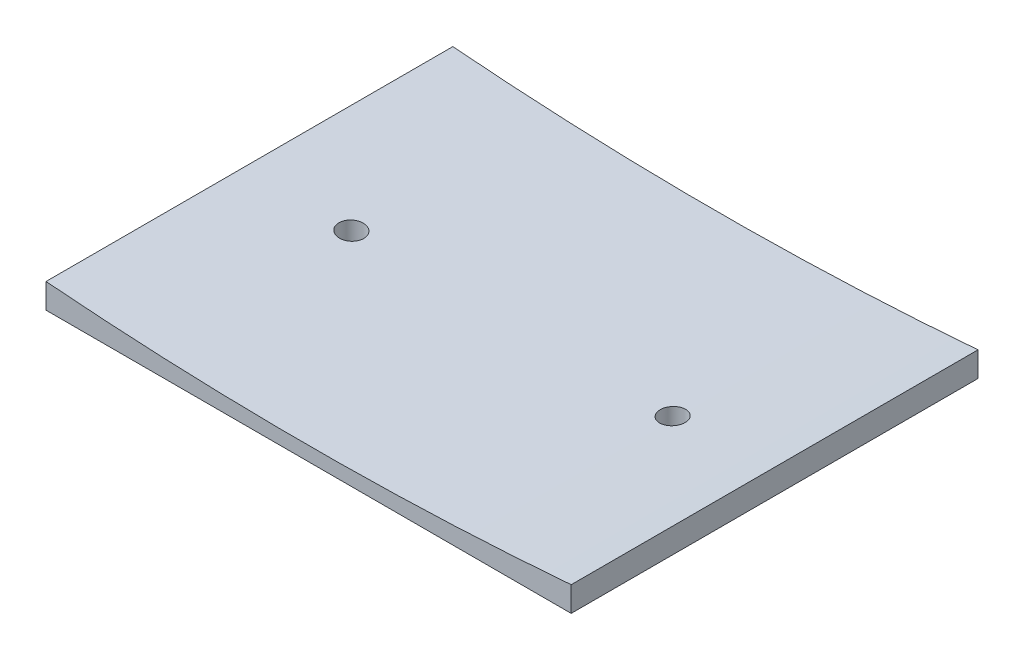
SolidWorks part; units mm, degrees
ref_plane "Alzado" through (0, 0, 0) normal (0, 0, 1) x (1, 0, 0)
ref_plane "Planta" through (0, 0, 0) normal (0, 1, 0) x (1, 0, 0)
ref_plane "Vista lateral" through (0, 0, 0) normal (1, 0, 0) x (0, 0, -1)
sketch "Croquis1" plane through (0, 0, 0) normal (0, 1, 0) x (1, 0, 0)
  line L1 (-18.6005, 9.0703) -> (34.1995, 9.0703)
  line L2 (-18.6005, 9.0703) -> (-18.6005, -31.8297)
  line L3 (-18.6005, -31.8297) -> (34.1995, -31.8297)
  line L4 (34.1995, 9.0703) -> (34.1995, -31.8297)
  dimension "D1" = 52.8
  dimension "D2" = 40.9
extrude "Saliente-Extruir1" add sketch "Croquis1" along normal blind 2.5
sketch "Croquis2" plane through (0, 0, 31.8297) normal (0, 0, 1) x (1, 0, 0)
  line L0 (-18.6005, 2.5) -> (34.1995, 2.5)
  arc A0 (-18.6005, 2.5) -> (34.1995, 2.5) centre (7.7995, 325.2085) ccw
extrude "Cortar-Extruir1" cut sketch "Croquis2" against normal blind 44
sketch "Croquis3" plane through (0, 0, 0) normal (0, -1, 0) x (1, 0, 0)
  line L0 (34.1995, 11.3797) -> (23.9495, 11.3797) construction
  line L1 (34.1995, 31.8297) -> (34.1995, -9.0703) construction
  line L2 (7.7995, 31.8297) -> (7.7995, -9.0703) construction
  line L3 (-18.6005, 31.8297) -> (34.1995, 31.8297) construction
  line L4 (34.1995, -9.0703) -> (-18.6005, -9.0703) construction
  circle A0 centre (23.9495, 11.3797) radius 1.25
  circle A1 centre (-8.3505, 11.3797) radius 1.25
  dimension "D2" = 2.5
  dimension "D1" = 10.25
extrude "Cortar-Extruir2" cut sketch "Croquis3" against normal blind 44
